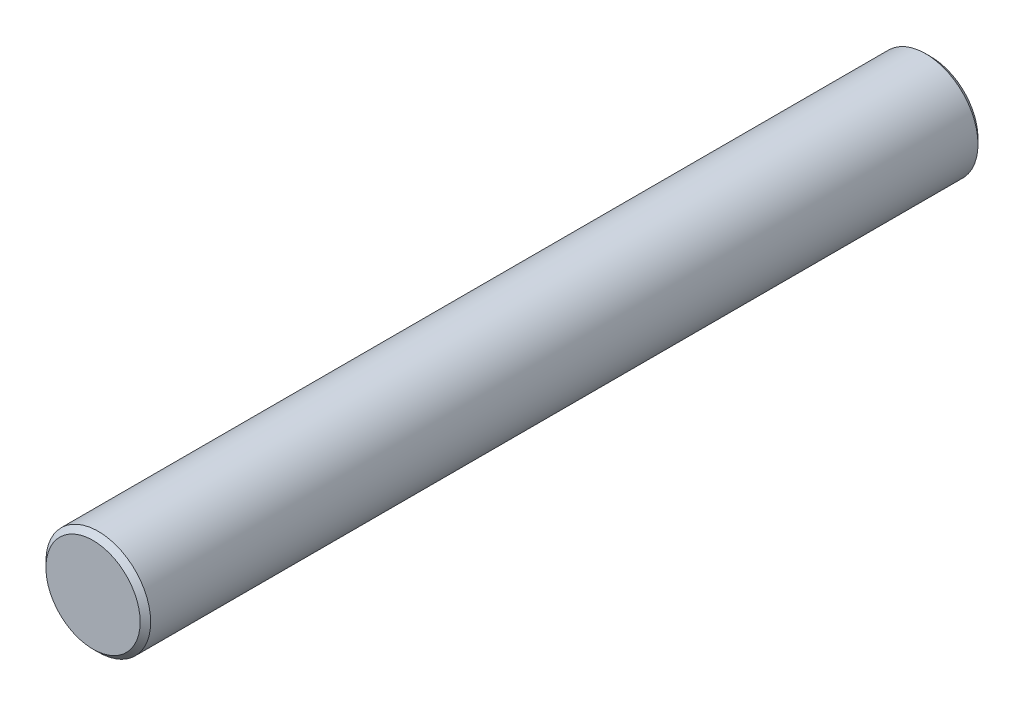
SolidWorks part; units mm, degrees
ref_plane "Front Plane" through (0, 0, 0) normal (0, 0, 1) x (1, 0, 0)
ref_plane "Top Plane" through (0, 0, 0) normal (0, 1, 0) x (1, 0, 0)
ref_plane "Right Plane" through (0, 0, 0) normal (1, 0, 0) x (0, 0, -1)
sketch "Sketch2" plane through (0, 0, 0) normal (0, 0, 1) x (1, 0, 0)
  circle A0 centre (0, 0) radius 1.5
  dimension "D1" = 3
extrude "Boss-Extrude1" add sketch "Sketch2" along normal blind 24
chamfer "Chamfer1" distance 0.15 angle 45 2 edges at (1.5, 0, 24) (1.5, 0, 0)
